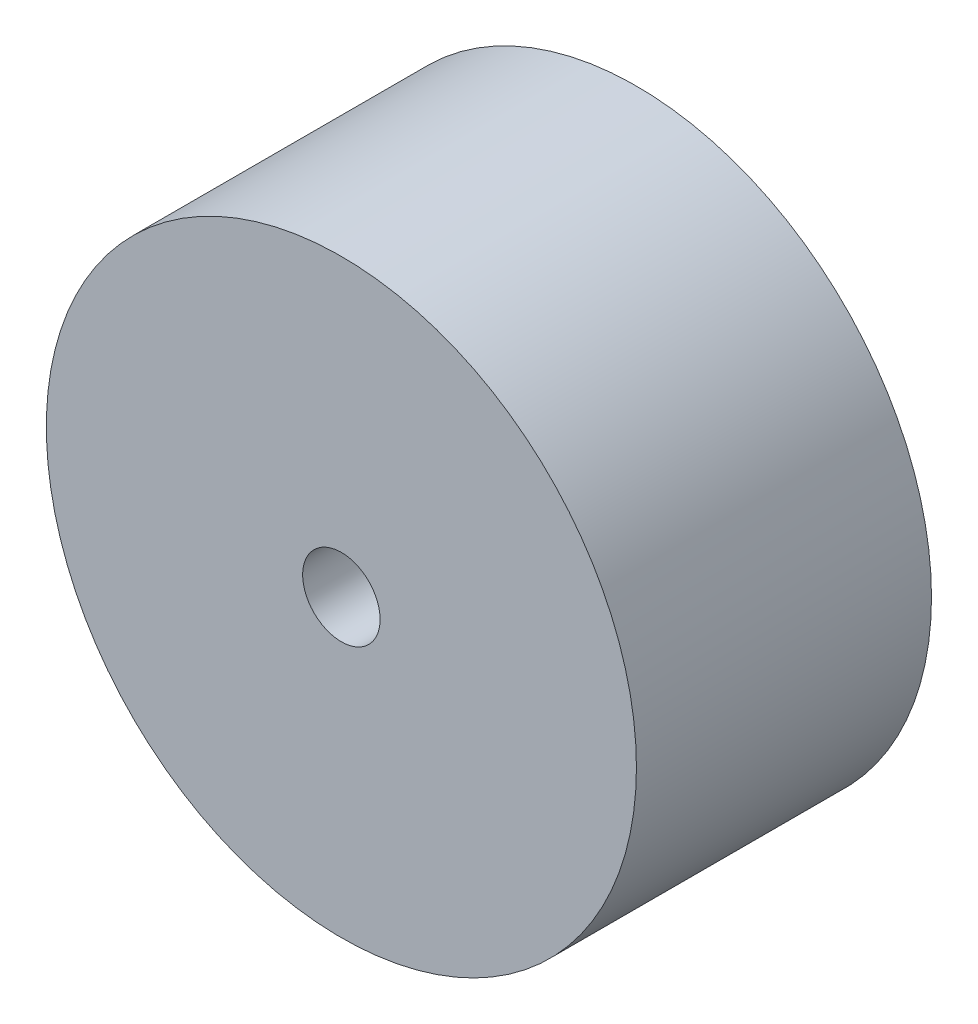
SolidWorks part; units mm, degrees
ref_plane "Front Plane" through (0, 0, 0) normal (0, 0, 1) x (1, 0, 0)
ref_plane "Top Plane" through (0, 0, 0) normal (0, 1, 0) x (1, 0, 0)
ref_plane "Right Plane" through (0, 0, 0) normal (1, 0, 0) x (0, 0, -1)
sketch "Sketch1" plane through (0, 0, 0) normal (0, 0, 1) x (1, 0, 0)
  circle A0 centre (0, 0) radius 19.05
  circle A1 centre (0, 0) radius 2.5
  dimension "D1" = 38.1
  dimension "D2" = 5
extrude "Boss-Extrude1" add sketch "Sketch1" along normal blind 19.05 contours A0 A1
